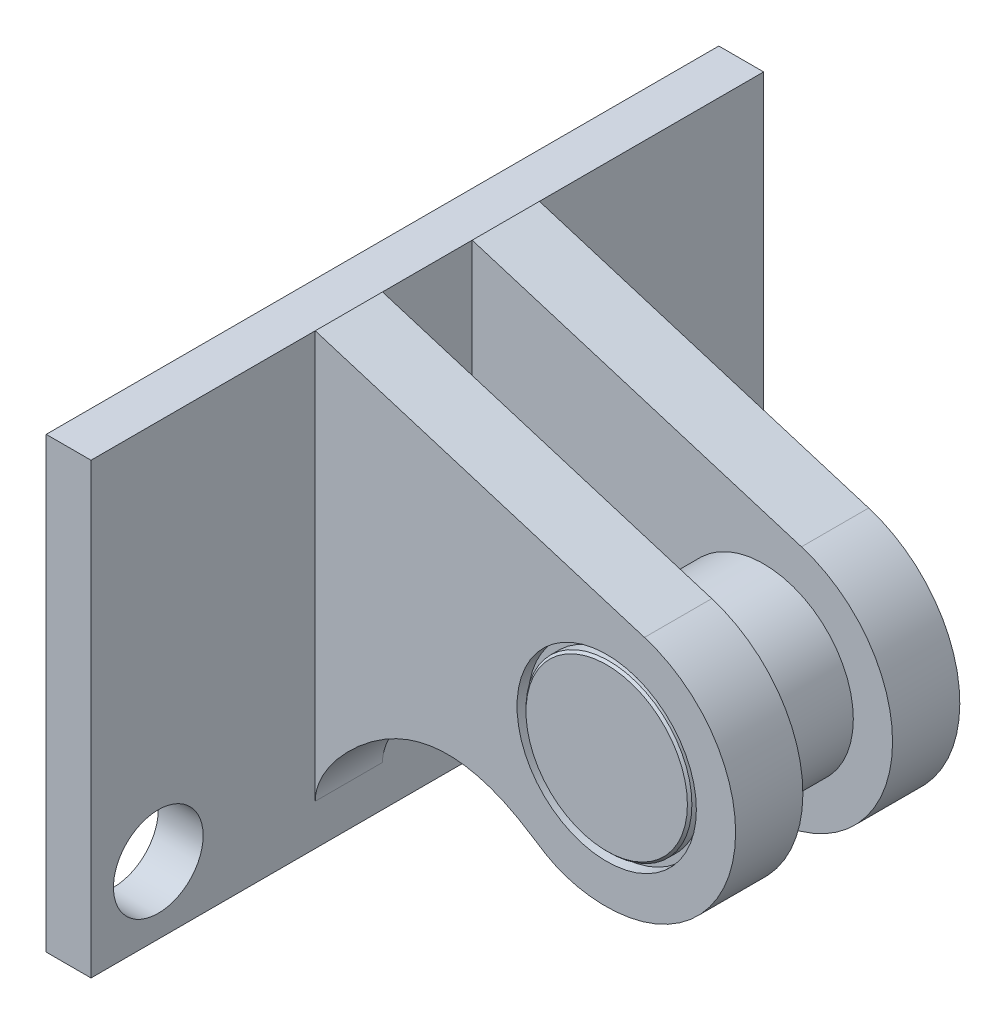
SolidWorks part; units mm, degrees
ref_plane "Alzado" through (0, 0, 0) normal (0, 0, 1) x (1, 0, 0)
ref_plane "Planta" through (0, 0, 0) normal (0, 1, 0) x (1, 0, 0)
ref_plane "Vista lateral" through (0, 0, 0) normal (1, 0, 0) x (0, 0, -1)
sketch "Croquis1" plane through (0, 0, 0) normal (0, 0, 1) x (1, 0, 0)
sketch_block_instance "chumacera-2"
sketch_block "chumacera" parameters "D1"=8, "D2"=12, "D3"=7
ref_plane "Plano1" through (4.6598, 0, 0) normal (1, 0, 0) x (0, 0, -1)
sketch "Croquis2" plane through (4.6598, 0, 0) normal (1, 0, 0) x (0, 0, -1)
  line L1 (-15, -22.0058) -> (15, -22.0058)
  line L2 (-15, -22.0058) -> (-15, -2.0058)
  line L3 (-15, -2.0058) -> (15, -2.0058)
  line L4 (15, -22.0058) -> (15, -2.0058)
  line L5 (-15, -22.0058) -> (15, -2.0058) construction
  line L6 (-15, -2.0058) -> (15, -22.0058) construction
  point P0 (0, -12.0058)
  point P2 (0, -12.0058)
  dimension "D1" = 30
  dimension "D2" = 20
extrude "Saliente-Extruir1" add sketch "Croquis2" along normal blind 2
ref_plane "Plano2" through (0, 0, 2) normal (0, 0, 1) x (1, 0, 0)
sketch "Croquis3" plane through (0, 0, 2) normal (0, 0, 1) x (1, 0, 0)
  line L1 (4.6598, -12.0058) -> (19.6598, -12.0058) construction
  line L2 (6.6598, -2.0058) -> (6.6598, -22.0058) construction
  line L3 (6.6598, -2.0058) -> (6.6598, -20.1789)
  line L4 (6.6598, -2.0058) -> (21.3453, -6.5084)
  line L5 (6.6598, -20.1789) -> (20.6748, -17.6655) construction
  line L6 (6.6598, -2.0058) -> (4.6598, -2.0058) construction
  circle A1 centre (19.6598, -12.0058) radius 4
  circle A2 centre (19.6598, -12.0058) radius 5.75 construction
  arc A3 (20.6748, -17.6655) -> (21.3453, -6.5084) centre (19.6598, -12.0058) ccw
  spline S0 degree 3 poles (20.6748, -17.6655) (19.5349, -17.8699) (17.7927, -17.715) (14.4778, -15.3673) (10.5194, -14.5252) (6.6598, -19.0081) (6.6598, -20.1789) knots 0 0 0 0 0.229346 0.306026 0.766799 1 1 1 1
  dimension "D1" = 5.75
  dimension "D4" = 8
  dimension "D2" = 10
  dimension "D3" = 13
  dimension "D5" = 8.1731
extrude "Saliente-Extruir2" add sketch "Croquis3" along normal blind 3 contours L5 A3 L4 L3 A1
mirror "Simetría1" about plane through (0, 0, 0) normal (0, 0, 1) of "Saliente-Extruir2"
sketch "Croquis4" plane through (6.6598, 0, 0) normal (1, 0, 0) x (0, 0, -1)
  line L0 (-15, -22.0058) -> (15, -22.0058) construction
  line L1 (-15, -2.0058) -> (-15, -22.0058) construction
  circle A0 centre (-12, -19.0058) radius 2
  dimension "D1" = 3
  dimension "D3" = 4
  dimension "D2" = 3
extrude "Cortar-Extruir1" cut sketch "Croquis4" against normal up to next
sketch "Croquis5" plane through (0, 0, 5) normal (0, 0, 1) x (1, 0, 0)
  circle A0 centre (19.6598, -12.0058) radius 4 construction
  circle A1 centre (19.6598, -12.0058) radius 4
extrude "Saliente-Extruir3" add sketch "Croquis5" against normal up to surface (10 mm away) separate body up to face at (16.6841, -11.3414, -5)
sketch "Croquis6" plane through (0, 0, 5) normal (0, 0, 1) x (1, 0, 0)
  circle A0 centre (19.6598, -12.0058) radius 4 construction
  circle A1 centre (19.6598, -12.0058) radius 4
  circle A2 centre (19.6598, -12.0058) radius 3.7
  dimension "D1" = 0.3
extrude "Cortar-Extruir2" cut sketch "Croquis6" against normal blind 0.5
chamfer "Chaflán1" distance 0.1 angle 45 1 edges at (23.3598, -12.0058, 5)
mirror "Simetría3" about plane through (0, 0, 0) normal (0, 0, 1) of "Cortar-Extruir2"
chamfer "Chaflán2" distance 0.1 angle 45 1 edges at (23.3598, -12.0058, -5)
